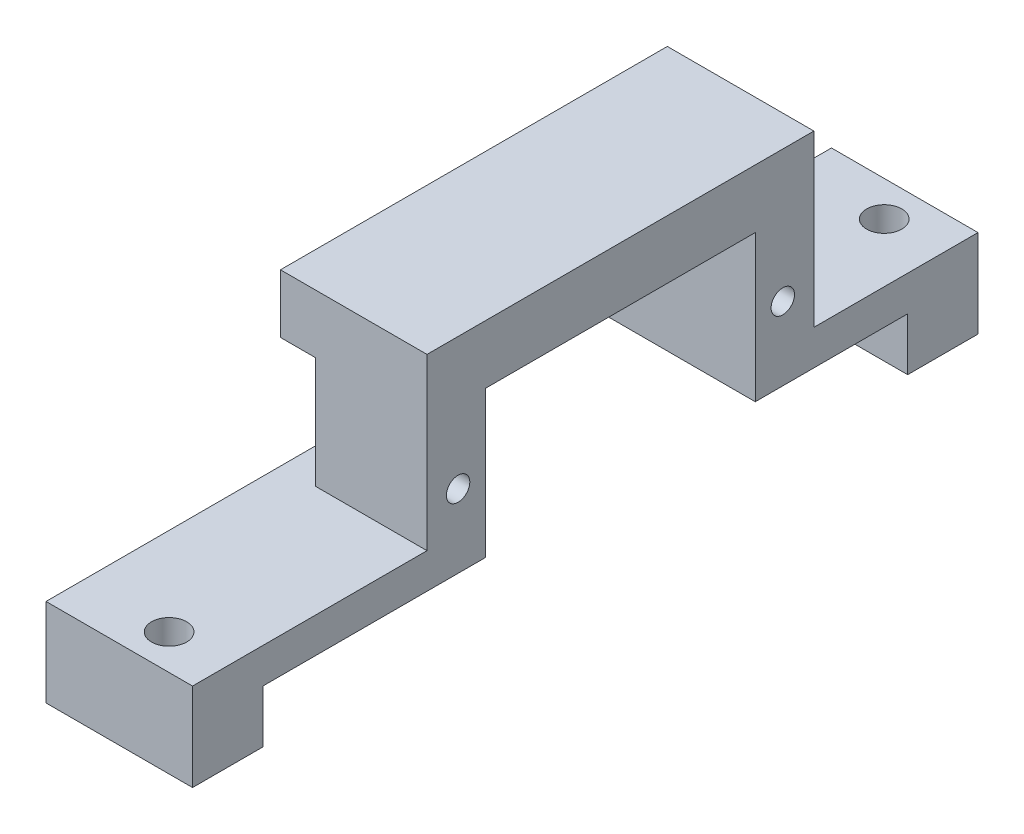
SolidWorks part; units mm, degrees
ref_plane "Front Plane" through (0, 0, 0) normal (0, 0, 1) x (1, 0, 0)
ref_plane "Top Plane" through (0, 0, 0) normal (0, 1, 0) x (1, 0, 0)
ref_plane "Right Plane" through (0, 0, 0) normal (1, 0, 0) x (0, 0, -1)
sketch "Sketch2" plane through (0, 0, 0) normal (1, 0, 0) x (0, 0, -1)
  line L0 (6, 0) -> (25, 0)
  line L1 (0, 3) -> (20, 3)
  line L2 (25, 0) -> (25, 12.5)
  line L3 (25, 12.5) -> (48, 12.5)
  line L4 (48, 12.5) -> (48, 0)
  line L5 (53, 3) -> (67, 3)
  line L6 (0, 3) -> (67, 3) construction
  line L7 (20, 3) -> (20, 17.5)
  line L8 (20, 17.5) -> (53, 17.5)
  line L9 (53, 17.5) -> (53, 3)
  line L10 (0, 3) -> (0, 0)
  line L11 (67, 3) -> (67, 0)
  line L12 (20, 0) -> (20, 17.5) construction
  line L13 (53, 17.5) -> (53, 0) construction
  line L14 (48, 0) -> (61, 0)
  line L15 (0, 0) -> (67, 0) construction
  line L16 (0, 0) -> (0, -4.5)
  line L17 (0, -4.5) -> (6, -4.5)
  line L18 (6, -4.5) -> (6, 0)
  line L19 (61, -4.5) -> (67, -4.5)
  line L20 (67, -4.5) -> (67, 0)
  line L21 (61, -4.5) -> (61, 0)
  dimension "D1" = 67
  dimension "D3" = 23
  dimension "D4" = 19
  dimension "D5" = 12.5
  dimension "D7" = 4.5
  dimension "D8" = 6
  dimension "D9" = 6
  dimension "D2" = 3
  dimension "D6" = 5
extrude "Boss-Extrude1" add sketch "Sketch2" along normal blind 12.5
sketch "Sketch3" plane through (0, 3, 0) normal (0, 1, 0) x (1, 0, 0)
  line L0 (12.5, 0) -> (0, 0) construction
  line L1 (12.5, 20) -> (12.5, 0) construction
  line L2 (12.5, 0) -> (12.5, 67) construction
  line L3 (12.5, 33.5) -> (7.5, 33.5) construction
  circle A0 centre (7.5, 3) radius 1.5
  circle A1 centre (7.5, 64) radius 1.5
  dimension "D1" = 3
  dimension "D2" = 3
  dimension "D3" = 5
extrude "Cut-Extrude1" cut sketch "Sketch3" against normal blind 12.5
sketch "Sketch4" plane through (0, 0, -20) normal (0, 0, 1) x (1, 0, 0)
  line L7 (12.5, 12.5) -> (0, 12.5) construction
  line L8 (0, 3) -> (3, 3)
  line L9 (0, 3) -> (0, 12.5)
  line L10 (0, 12.5) -> (3, 12.5)
  line L11 (3, 3) -> (3, 12.5)
  dimension "D1" = 3
extrude "Cut-Extrude2" cut sketch "Sketch4" against normal blind 5
sketch "Sketch5" plane through (12.5, 0, 0) normal (1, 0, 0) x (0, 0, -1)
  line L0 (25, 6.25) -> (48, 6.25) construction
  line L1 (25, 0) -> (25, 12.5) construction
  line L2 (48, 12.5) -> (48, 0) construction
  line L3 (36.5, 8.3791) -> (36.5, 3.9308) construction
  circle A0 centre (22.65, 6.25) radius 1
  circle A1 centre (50.35, 6.25) radius 1
  dimension "D1" = 2
  dimension "D2" = 13.85
extrude "Cut-Extrude3" cut sketch "Sketch5" against normal blind 3
